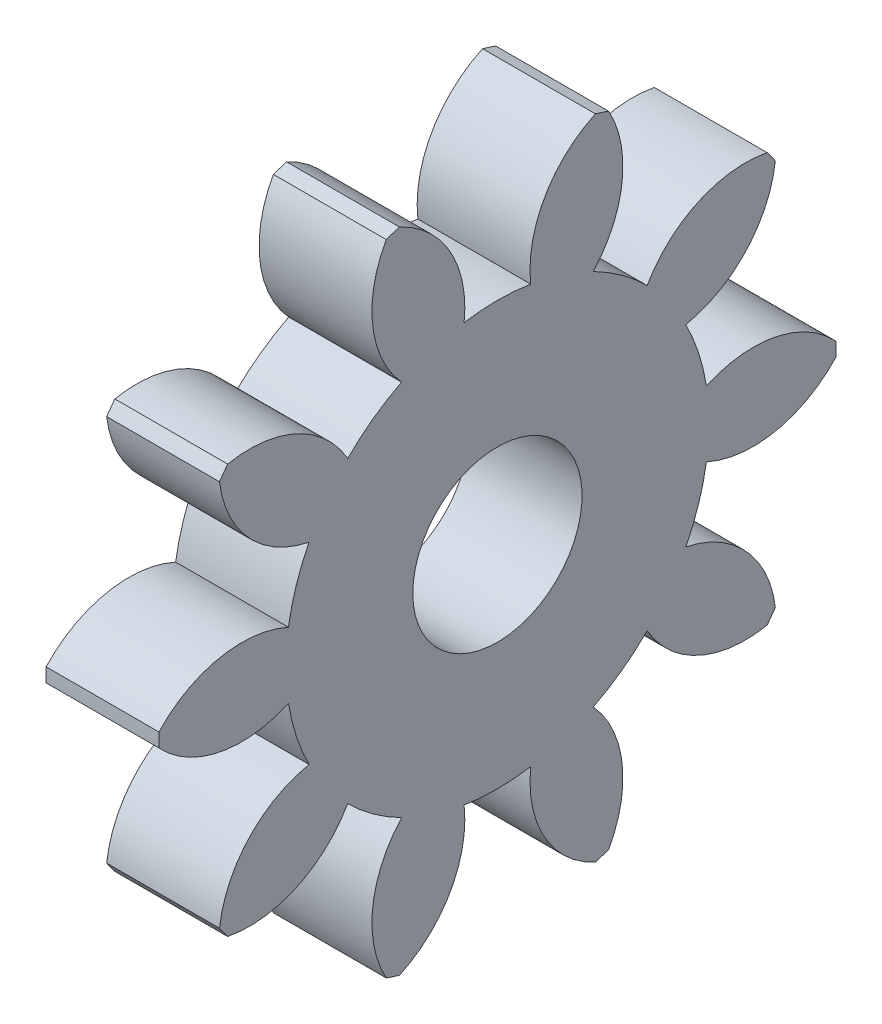
SolidWorks part; units mm, degrees
ref_plane "Plane1" through (0, 0, 0) normal (0, 0, 1) x (1, 0, 0)
ref_plane "Plane2" through (0, 0, 0) normal (0, 1, 0) x (1, 0, 0)
ref_plane "Plane3" through (0, 0, 0) normal (1, 0, 0) x (0, 0, -1)
sketch "HoldingSke" plane through (0, 0, 0) normal (0, 1, 0) x (1, 0, 0)
  line L0 (0, 0) -> (400.2259, -70.5706)
  line L1 (-15, 0) -> (100, 0) construction
  line L2 (0, 0) -> (-2.1039, 2.3779)
  line L3 (0, 0) -> (-11.863, 4.5341)
  line L4 (0, 0) -> (8.5048, 1.4996)
  line L5 (0, 0) -> (-47.5972, -17.7524)
  line L6 (0, 0) -> (-2.632, -1.7758)
  line L7 (-2.1039, 2.3779) -> (8.8308, 51.9871)
  line L8 (-76.2, 54.61) -> (-71.1708, 54.61)
  line L9 (-71.009, 38.7566) -> (-53.1078, 45.2721)
  line L10 (-76.2, 71.12) -> (104.1128, 71.12)
  line L11 (0, 0) -> (-3.175, 0)
  line L12 (-76.2, 101.6) -> (-76.1428, 101.6)
  line L13 (24.9733, 27.94) -> (52.9518, 28.4284)
  line L14 (24.9733, 27.94) -> (24.9746, 27.94)
  line L15 (24.9733, 27.94) -> (100.4006, 29.5858)
  circle A0 centre (0, 0) radius 2.3813
  circle A1 centre (0, 0) radius 5.9519
  circle A2 centre (0, 0) radius 38.1
  circle A3 centre (0, 0) radius 2.3813
sketch "BasProSke" plane through (0, 0, 0) normal (0, 1, 0) x (1, 0, 0)
  line L0 (-10, 0) -> (60, 0) construction
  line L1 (0, 0) -> (0, 9.525)
  line L2 (0, 0) -> (3.175, 0)
  line L3 (3.175, 0) -> (3.175, 9.525)
  line L4 (3.175, 9.525) -> (0, 9.525)
revolve "Base-Revolve" add sketch "BasProSke" angle 360 about L0
sketch "TooCutSke" plane through (0, 0, 0) normal (1, 0, 0) x (0, 0, -1)
  line L1 (0, 0) -> (0, 107) construction
  line L2 (0, 0) -> (-1.3415, 7.8233) construction
  line L3 (0, 0) -> (-4.8546, 14.941) construction
  line L4 (-1.3415, 7.8233) -> (-2.4273, 7.4705) construction
  arc A0 (0.9368, 5.8777) -> (-0.9368, 5.8777) centre (0, 0) ccw
  arc A1 (2.7918, 9.1332) -> (-2.7918, 9.1332) centre (0, 0) ccw
  circle A2 centre (0, 0) radius 7.9375 construction
  circle A3 centre (0, 0) radius 7.4588 construction
  arc A4 (-0.9368, 5.8777) -> (-2.7918, 9.1332) centre (-4.0915, 6.2365) ccw
  arc A5 (2.7918, 9.1332) -> (0.9368, 5.8777) centre (4.0915, 6.2365) ccw
extrude "ToothCut" cut sketch "TooCutSke" along normal through all
fillet "Breaks" [suppressed] radius 0.0318
fillet "RootFillets" [suppressed] radius 0.3981
pattern_circular "TeethCuts" count 10 every 36 about axis through (-10, 0, 0) along (1, 0, 0) of "ToothCut", "RootFillets", "Breaks"
sketch "HubNeaOneSke" plane through (0, 0, 0) normal (-1, 0, 0) x (0, 0, 1)
  circle A0 centre (0, 0) radius 5.9519
extrude "HubNearOne" [suppressed] add sketch "HubNeaOneSke" along normal blind 47.6251
sketch "HubNeaBotSke" plane through (0, 0, 0) normal (-1, 0, 0) x (0, 0, 1)
  circle A0 centre (0, 0) radius 5.9519
extrude "HubNearBoth" [suppressed] add sketch "HubNeaBotSke" along normal blind 23.8125
ref_plane "FarPln" through (3.175, 0, 0) normal (1, 0, 0) x (0, 0, -1)
sketch "HubFarSke" plane through (3.175, 0, 0) normal (1, 0, 0) x (0, 0, -1)
  circle A0 centre (0, 0) radius 5.9519
extrude "HubFar" [suppressed] add sketch "HubFarSke" along normal blind 23.8125
sketch "BorSke" plane through (0, 0, 0) normal (1, 0, 0) x (0, 0, -1)
  circle A0 centre (0, 0) radius 2.3813
extrude "Bore" cut sketch "BorSke" along normal mid plane 101.6001
sketch "KeySke" plane through (0, 0, 0) normal (1, 0, 0) x (0, 0, -1)
  line L0 (-0.127, 0) -> (-0.127, 2.648)
  line L1 (-0.127, 2.648) -> (0.127, 2.648)
  line L2 (0.127, 2.648) -> (0.127, 0)
  line L3 (0, 0) -> (0, 34) construction
  line L4 (-0.127, 0) -> (0.127, 0)
extrude "Keyway" [suppressed] cut sketch "KeySke" along normal mid plane 101.6001
pattern_circular "Keyway2" [suppressed] count 2 every 90 about axis through (-10, 0, 0) along (1, 0, 0)
equation "' \"Pitch@HoldingSke\" = 4"
equation "' \"Num_teeth@HoldingSke\" = 12"
equation "' \"Ap@HoldingSke\" =  20"
equation "' \"Ap@HoldingSke\" = 20"
equation "' \"Width@HoldingSke\" = 0.5"
equation "' \"Hub_dia@HoldingSke\"= 1"
equation "' \"Hub_dia@HoldingSke\" = 1"
equation "' \"Overall_len@HoldingSke\" = 1.0"
equation "' \"Bore@HoldingSke\" = 0.75"
equation "' \"T_dim@HoldingSke\" = 0.85"
equation "' \"Width@KeySke\" = 0.25"
equation "' \"Show_teeth@HoldingSke\" = 13"
equation "' \"Backlash@HoldingSke\" = 0.009"
equation "' \"Addendum_fac@HoldingSke\" = 1.0"
equation "' \"Dedendum_fac@HoldingSke\" = 1.25"
equation "' \"Dedendum_add@HoldingSke\" = 0.00005"
equation "' \"Clearance_fac@HoldingSke\" = 0.25"
equation "' \"Pitch@HoldingSke\" = 0.5"
equation "' \"Num_teeth@HoldingSke\" = 23"
equation "' \"Show_teeth@HoldingSke\" = 23"
equation "' \"Backlash@HoldingSke\" = 0.0375"
equation "\"Overcut_dia@TooCutSke\" = (\"Num_teeth@HoldingSke\" + 2 * \"Addendum_fac@HoldingSke\") / \"Pitch@HoldingSke\" + 0.002"
equation "\"Pitch_dia@TooCutSke\" = \"Num_teeth@HoldingSke\" / \"Pitch@HoldingSke\""
equation "\"Base_dia@TooCutSke\" = \"Num_teeth@HoldingSke\" / \"Pitch@HoldingSke\" * cos((\"Ap@HoldingSke\"  * 3.14159265 / 180))"
equation "\"Root_dia@TooCutSke\" = (\"Num_teeth@HoldingSke\" + 2) / \"Pitch@HoldingSke\" - 2 * (\"Addendum_fac@HoldingSke\" + \"Dedendum_fac@HoldingSke\") / \"Pitch@HoldingSke\" - \"Dedendum_add@HoldingSke\" * 2"
equation "\"Half_ang@TooCutSke\" = 180 / \"Num_teeth@HoldingSke\""
equation "\"Half_CT@TooCutSke\" = \"Num_teeth@HoldingSke\" / \"Pitch@HoldingSke\" * sin((3.14159265 / 2 / \"Num_teeth@HoldingSke\")) / 2 - 7 * \"Backlash@HoldingSke\" / 4"
equation "\"Flank_rad@TooCutSke\" = \"Num_teeth@HoldingSke\" / \"Pitch@HoldingSke\" / 5"
equation "\"Radius@RootFillets\" = \"Clearance_fac@HoldingSke\" / \"Pitch@HoldingSke\" + \"Dedendum_add@HoldingSke\""
equation "\"Break_rad@Breaks\" = 0.02 / \"Pitch@HoldingSke\""
equation "\"Thickness@HoldingSke\" = \"Width@HoldingSke\""
equation "\"OAL@HoldingSke\" = \"Thickness@HoldingSke\""
equation "\"MHD@HoldingSke\" = (\"Num_teeth@HoldingSke\" + 2) / \"Pitch@HoldingSke\" - 2 * (\"Addendum_fac@HoldingSke\" + \"Dedendum_fac@HoldingSke\")  / \"Pitch@HoldingSke\" - \"Dedendum_add@HoldingSke\" * 2"
equation "\"MBD@HoldingSke\" = (\"Num_teeth@HoldingSke\" + 2) / \"Pitch@HoldingSke\" - 2 * (\"Addendum_fac@HoldingSke\" + \"Dedendum_fac@HoldingSke\")  / \"Pitch@HoldingSke\" - \"Dedendum_add@HoldingSke\" * 2 - 0.002"
equation "\"MHD@HoldingSke\" = ((sgn( \"MHD@HoldingSke\" - \"Hub_dia@HoldingSke\" )-1)*( \"MHD@HoldingSke\" - \"Hub_dia@HoldingSke\" ))/-2+ \"Hub_dia@HoldingSke\""
equation "\"MBD@HoldingSke\" = ((sgn( \"MBD@HoldingSke\" - \"Bore@HoldingSke\" )-1)*( \"MBD@HoldingSke\" - \"Bore@HoldingSke\" ))/-2+ \"Bore@HoldingSke\""
equation "\"OAL@HoldingSke\" = ((sgn( \"OAL@HoldingSke\" - \"Overall_len@HoldingSke\" )+1)*( \"OAL@HoldingSke\" - \"Overall_len@HoldingSke\" ))/2 + \"Overall_len@HoldingSke\" + 0.000002"
equation "\"Num_teeth@TeethCuts\" = int( \"Show_teeth@HoldingSke\" ) + 1"
equation "\"Num_teeth@TeethCuts\" = ((sgn( \"Num_teeth@TeethCuts\" - \"Num_teeth@HoldingSke\" )-1)*( \"Num_teeth@TeethCuts\" - \"Num_teeth@HoldingSke\" ))/-2+ \"Num_teeth@HoldingSke\""
equation "\"Num_teeth@TeethCuts\" = ((sgn( \"Num_teeth@TeethCuts\" - 2.0)+1)*( \"Num_teeth@TeethCuts\" - 2.0))/2 +2.0"
equation "\"Angle@TeethCuts\" = 360.0 / \"Num_teeth@HoldingSke\""
equation "\"Diameter@BasProSke\" = (\"Num_teeth@HoldingSke\" + 2 * \"Addendum_fac@HoldingSke\") / \"Pitch@HoldingSke\""
equation "\"Thickness@BasProSke\"  = \"Thickness@HoldingSke\""
equation "' \"Fillet_rad@BasProSke\" =  \"Thickness@HoldingSke\" * 0.05"
equation "' \"Fillet_rad@BasProSke\" = \"Thickness@HoldingSke\" * 0.05"
equation "\"MHD@HoldingSke\" = ((sgn( \"MHD@HoldingSke\" - \"Root_dia@TooCutSke\" )-1)*( \"MHD@HoldingSke\" - \"Root_dia@TooCutSke\" ))/-2+ \"Root_dia@TooCutSke\""
equation "\"Diameter@HubNeaOneSke\" = \"MHD@HoldingSke\""
equation "\"Length@HubNearOne\" = \"OAL@HoldingSke\" - \"Thickness@BasProSke\""
equation "\"Diameter@HubNeaBotSke\" = \"MHD@HoldingSke\""
equation "\"Length@HubNearBoth\" = ( \"OAL@HoldingSke\" - \"Thickness@BasProSke\" ) / 2.0"
equation "\"Thickness@FarPln\" = \"Thickness@BasProSke\""
equation "\"Diameter@HubFarSke\" = \"MHD@HoldingSke\""
equation "\"Length@HubFar\" = ( \"OAL@HoldingSke\" - \"Thickness@BasProSke\" ) / 2.0"
equation "\"Diameter@BorSke\" = \"MBD@HoldingSke\""
equation "\"D1@Bore\" = \"OAL@HoldingSke\" * 2.0"
equation "\"D1@Keyway\" = \"OAL@HoldingSke\" * 2.0"
equation "\"Offset@KeySke\" = \"T_dim@HoldingSke\" - \"MBD@HoldingSke\" / 2.0"
